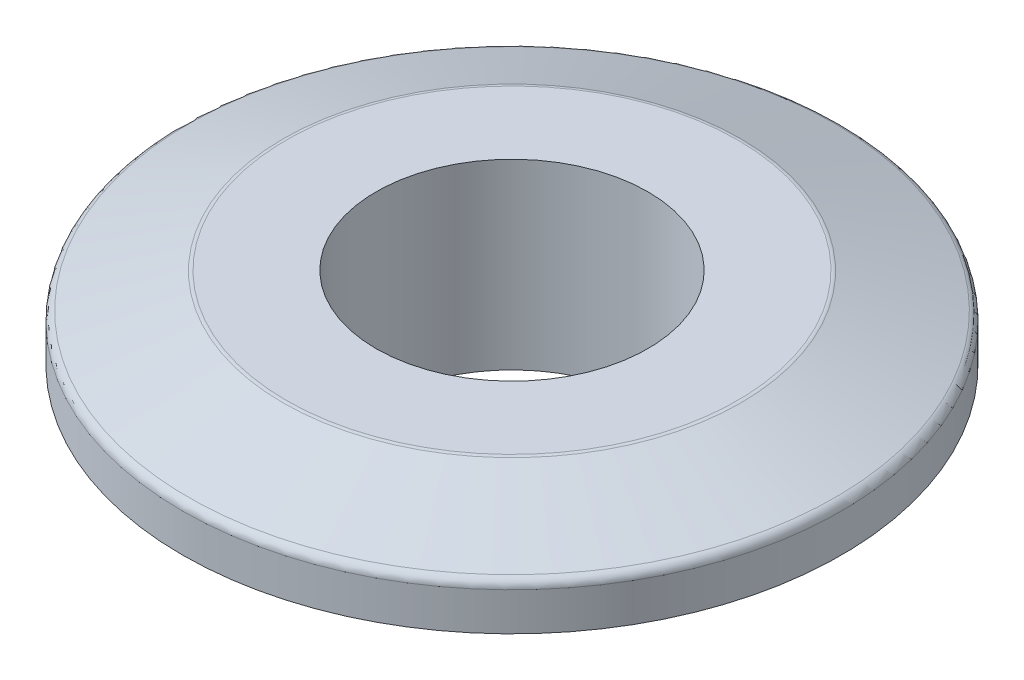
SolidWorks part; units mm, degrees
material "6061 Alloy"
ref_plane "Front Plane" through (0, 0, 0) normal (0, 0, 1) x (1, 0, 0)
ref_plane "Top Plane" through (0, 0, 0) normal (0, 1, 0) x (1, 0, 0)
ref_plane "Right Plane" through (0, 0, 0) normal (1, 0, 0) x (0, 0, -1)
sketch "Sketch1" plane through (0, 0, 0) normal (0, 1, 0) x (1, 0, 0)
  circle A0 centre (0, 0) radius 22.479
  circle A1 centre (0, 0) radius 9.271
  dimension "D1" = 44.958
  dimension "D2" = 18.542
extrude "Boss-Extrude1" add sketch "Sketch1" along normal blind 12.446
sketch "Sketch2" plane through (0, 0, 0) normal (0, -1, 0) x (1, 0, 0)
  circle A0 centre (0, 0) radius 12.7
  circle A1 centre (0, 0) radius 22.479 construction
  circle A2 centre (0, 0) radius 22.479
  dimension "D1" = 25.4
extrude "Cut-Extrude1" cut sketch "Sketch2" against normal blind 6.858
chamfer "Chamfer1" distance 2.54 angle 70 1 edges at (0, 12.446, 22.479)
chamfer "Chamfer2" distance 0.635 angle 45 1 edges at (0, 0, -12.7)
fillet "Fillet1" radius 0.635 2 edges at (0, 12.446, 15.5004) (0, 9.906, 22.479)
